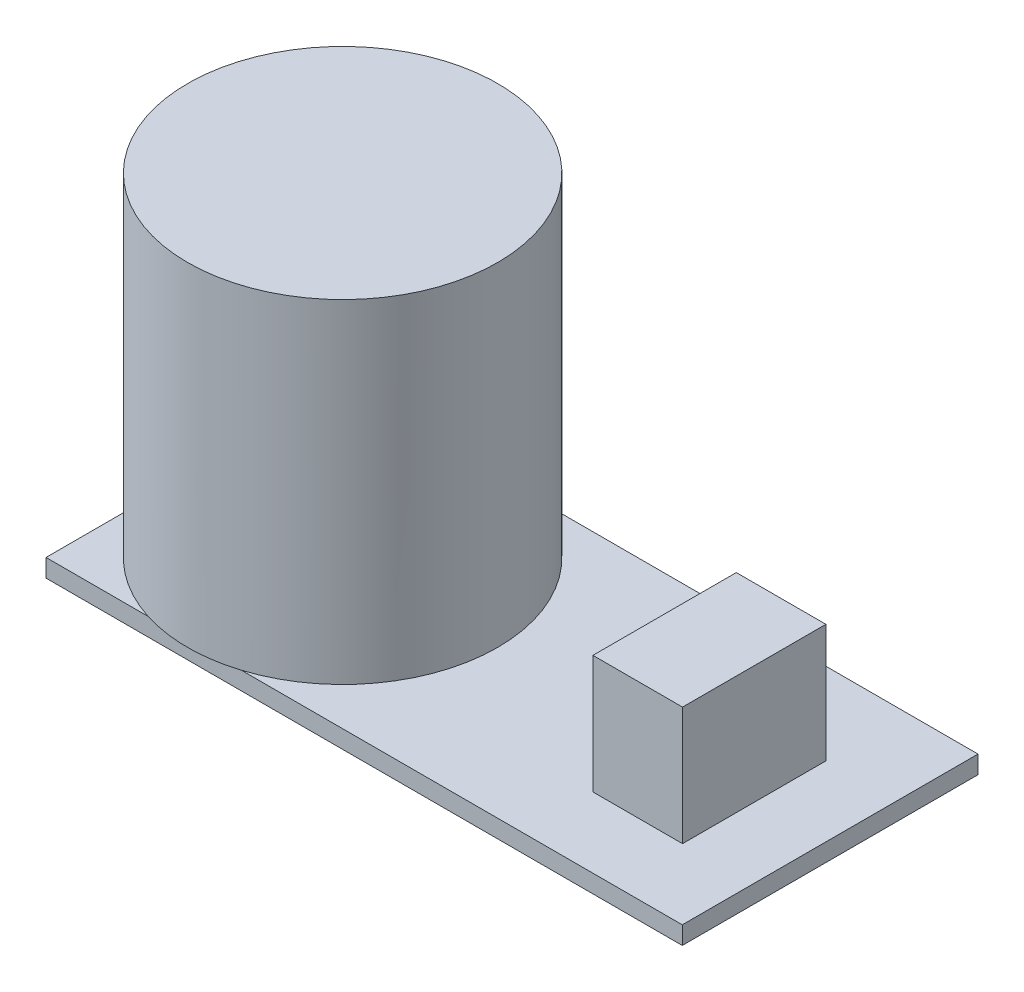
SolidWorks part; units mm, degrees
ref_plane "Front Plane" through (0, 0, 0) normal (0, 0, 1) x (1, 0, 0)
ref_plane "Top Plane" through (0, 0, 0) normal (0, 1, 0) x (1, 0, 0)
ref_plane "Right Plane" through (0, 0, 0) normal (1, 0, 0) x (0, 0, -1)
sketch "Sketch1" plane through (0, 0, 0) normal (0, 1, 0) x (1, 0, 0)
  line L0 (0, -8.25) -> (0, 42.2808) construction
  line L1 (-17.75, 8.25) -> (17.75, 8.25)
  line L2 (-17.75, 8.25) -> (-17.75, -8.25)
  line L3 (-17.75, -8.25) -> (17.75, -8.25)
  line L4 (17.75, 8.25) -> (17.75, -8.25)
  line L5 (17.75, 0) -> (-92.1538, 0) construction
  dimension "D1" = 35.5
  dimension "D2" = 16.5
extrude "Boss-Extrude1" add sketch "Sketch1" along normal blind 1
sketch "Sketch2" plane through (0, 1, 0) normal (0, 1, 0) x (1, 0, 0)
  line L0 (-17.75, 0) -> (25.7972, 0) construction
  line L1 (-17.75, 8.25) -> (-17.75, -8.25) construction
  circle A0 centre (-9.45, 0) radius 8.65
  dimension "D2" = 17.3
  dimension "D1" = 8.3
extrude "Boss-Extrude2" add sketch "Sketch2" along normal blind 18.6
sketch "Sketch3" plane through (0, 1, 0) normal (0, 1, 0) x (1, 0, 0)
  line L1 (13.8378, -4.3237) -> (8.8378, -4.3237)
  line L2 (13.8378, -4.3237) -> (13.8378, 3.6763)
  line L3 (13.8378, 3.6763) -> (8.8378, 3.6763)
  line L4 (8.8378, -4.3237) -> (8.8378, 3.6763)
  dimension "D1" = 8
  dimension "D2" = 5
extrude "Boss-Extrude3" add sketch "Sketch3" along normal blind 6.6
